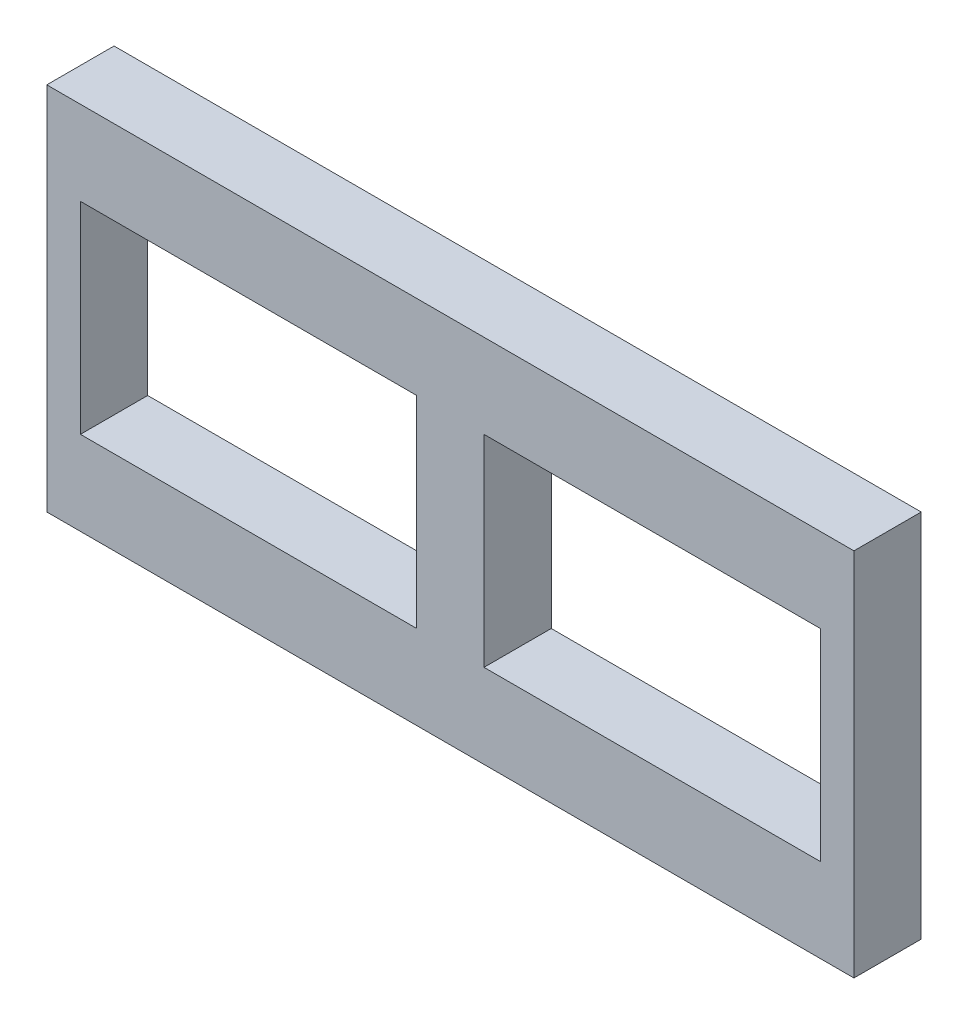
SolidWorks part; units mm, degrees
ref_plane "前基準面" through (0, 0, 0) normal (0, 0, 1) x (1, 0, 0)
ref_plane "上基準面" through (0, 0, 0) normal (0, 1, 0) x (1, 0, 0)
ref_plane "右基準面" through (0, 0, 0) normal (1, 0, 0) x (0, 0, -1)
sketch "草圖1" plane through (0, 0, 0) normal (0, 0, 1) x (1, 0, 0)
  line L0 (55, 0) -> (-55, 0) construction
  line L1 (-60, 27.5) -> (60, 27.5)
  line L2 (-60, 27.5) -> (-60, -27.5)
  line L3 (-60, -27.5) -> (60, -27.5)
  line L4 (60, 27.5) -> (60, -27.5)
  line L5 (0, -55) -> (0, 55) construction
  dimension "D1" = 55
  dimension "D2" = 120
  dimension "D3" = 27.5
  dimension "D4" = 60
extrude "填料-伸長1" add sketch "草圖1" along normal blind 10
sketch "草圖2" plane through (0, 0, 0) normal (0, 0, -1) x (-1, 0, 0)
  line L0 (-60, -27.5) -> (-60, 27.5) construction
  line L1 (-55, 15) -> (-5, 15)
  line L2 (-55, 15) -> (-55, -15)
  line L3 (-55, -15) -> (-5, -15)
  line L4 (-5, 15) -> (-5, -15)
  line L5 (-60, 27.5) -> (60, 27.5) construction
  line L6 (0, 55) -> (0, -55) construction
  line L7 (5, 15) -> (5, -15)
  line L8 (55, -15) -> (5, -15)
  line L9 (55, 15) -> (55, -15)
  line L10 (55, 15) -> (5, 15)
  dimension "D1" = 30
  dimension "D2" = 50
  dimension "D3" = 5
  dimension "D4" = 12.5
extrude "除料-伸長1" cut sketch "草圖2" against normal blind 10
